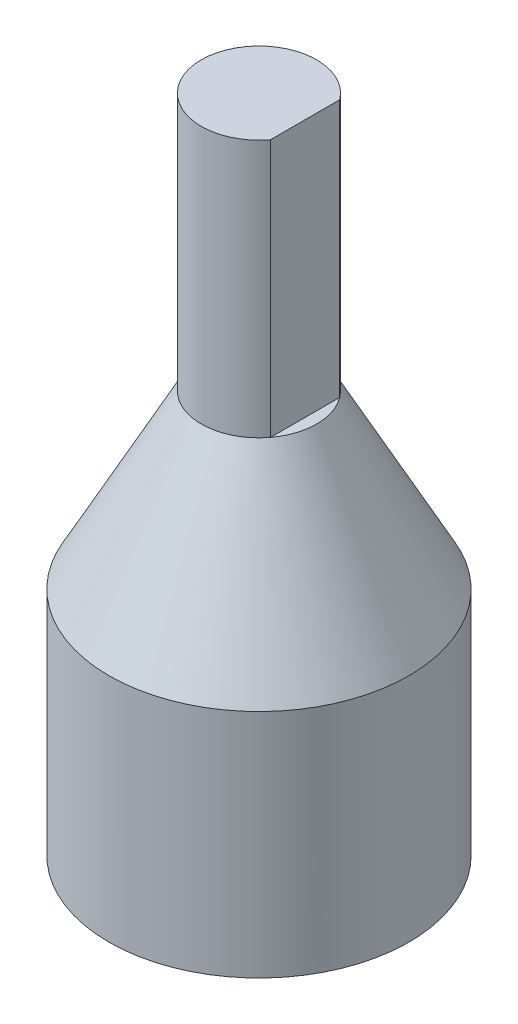
SolidWorks part; units mm, degrees
ref_plane "Front Plane" through (0, 0, 0) normal (0, 0, 1) x (1, 0, 0)
ref_plane "Top Plane" through (0, 0, 0) normal (0, 1, 0) x (1, 0, 0)
ref_plane "Right Plane" through (0, 0, 0) normal (1, 0, 0) x (0, 0, -1)
sketch "Sketch1" plane through (0, 0, 0) normal (0, 1, 0) x (1, 0, 0)
  line L4 (4.445, 0) -> (9.525, 0)
  line L5 (9.525, 0) -> (9.525, 10.16)
  line L6 (9.525, 10.16) -> (-0.635, 10.16)
  line L7 (-0.635, 10.16) -> (-0.635, 0)
  line L8 (-0.635, 0) -> (4.445, 0)
  circle A1 centre (4.445, 5.08) radius 8.255
  dimension "D3" = 16.51
  dimension "D1" = 5.08
  dimension "D2" = 10.16
  dimension "D4" = 10.16
  dimension "D5" = 10.16
extrude "Boss-Extrude1" add sketch "Sketch1" along normal blind 12.7
ref_plane "Plane2" through (0, 0, -5.08) normal (0, 0, -1) x (-1, 0, 0)
sketch "Sketch5" plane through (0, 0, -5.08) normal (0, 0, -1) x (-1, 0, 0)
  line L0 (-4.445, 12.7) -> (-4.445, 20.2461)
  line L1 (-9.525, 12.7) -> (0.635, 12.7) construction
  line L2 (-4.445, 36.336) -> (-4.445, 41.2035) construction
  line L3 (-12.7, 12.7) -> (-7.62, 22.1507)
  line L4 (-7.62, 22.1507) -> (-7.62, 36.336)
  line L5 (-7.62, 36.336) -> (-4.445, 36.336)
  line L6 (-4.445, 36.336) -> (-4.445, 12.7)
  line L7 (-12.7, 12.7) -> (-4.445, 12.7)
  dimension "D1" = 14.1853
revolve "Revolve4" add sketch "Sketch5" angle 360 about L2
sketch "Sketch6" plane through (0, 0, -5.08) normal (0, 0, -1) x (-1, 0, 0)
  line L0 (-7.62, 36.336) -> (-6.985, 36.336)
  line L3 (-1.27, 36.336) -> (-7.62, 36.336) construction
  line L5 (-6.985, 36.336) -> (-6.985, 22.1507)
  line L6 (-7.62, 22.1507) -> (-1.27, 22.1507) construction
  line L7 (-6.985, 22.1507) -> (-7.62, 22.1507)
  line L8 (-7.62, 22.1507) -> (-7.62, 36.336)
  dimension "D1" = 0.635
extrude "Cut-Extrude3" cut sketch "Sketch6" against normal blind 12.7 and the other way blind 12.7 contours L8 L0 L5 L7
